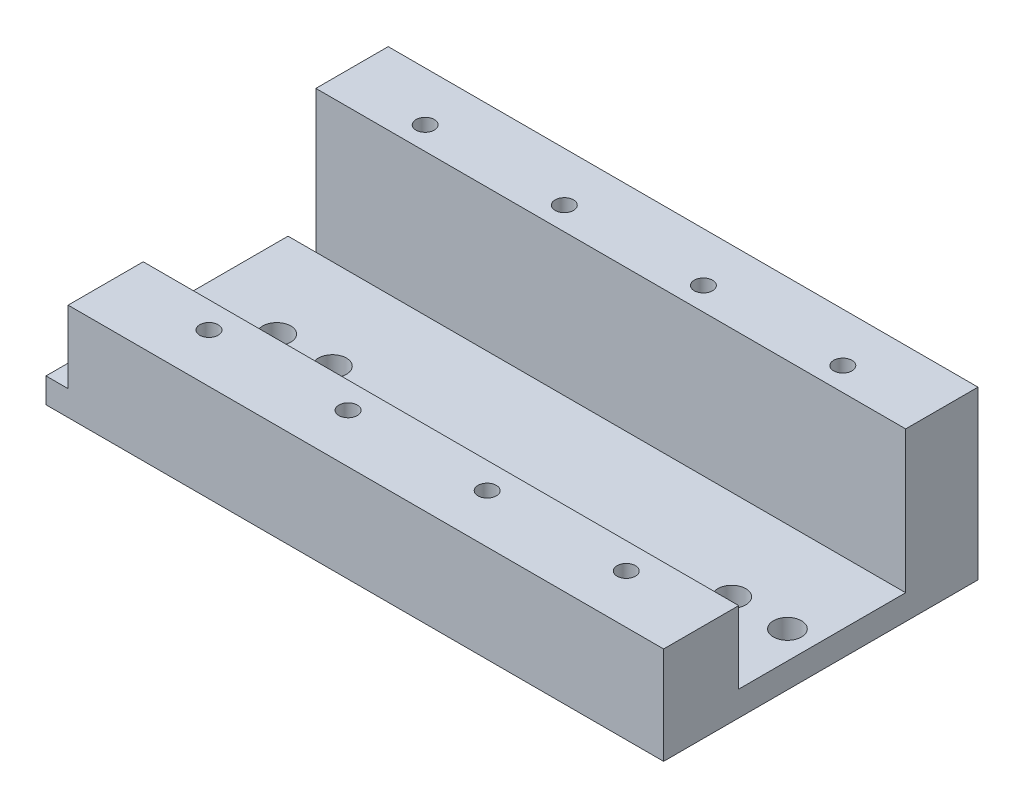
SolidWorks part; units mm, degrees
ref_plane "Front Plane" through (0, 0, 0) normal (0, 0, 1) x (1, 0, 0)
ref_plane "Top Plane" through (0, 0, 0) normal (0, 1, 0) x (1, 0, 0)
ref_plane "Right Plane" through (0, 0, 0) normal (1, 0, 0) x (0, 0, -1)
sketch "Sketch4" plane through (0, 0, 0) normal (0, 0, 1) x (1, 0, 0)
  line L1 (-89.891, -20.3228) -> (16.109, -20.3228)
  line L2 (-89.891, -20.3228) -> (-89.891, -50.3228)
  line L3 (-89.891, -50.3228) -> (16.109, -50.3228)
  line L4 (16.109, -20.3228) -> (16.109, -50.3228)
  dimension "D1" = 30
  dimension "D2" = 106
extrude "Boss-Extrude2" add sketch "Sketch4" against normal blind 13
sketch "Sketch25" plane through (0, 0, 0) normal (0, 0, 1) x (1, 0, 0)
  line L0 (-89.891, -20.3228) -> (-89.891, -50.3228) construction
  line L1 (-89.891, -24.6013) -> (16.109, -24.6013)
  line L2 (-89.891, -24.6013) -> (-89.891, -33.2013)
  line L3 (-89.891, -33.2013) -> (16.109, -33.2013)
  line L4 (16.109, -24.6013) -> (16.109, -33.2013)
  line L5 (16.109, -50.3228) -> (16.109, -20.3228) construction
  dimension "D1" = 8.6
hole_wizard "M4x0.7 Tapped Hole1" positions "3DSketch1" profile "Sketch27" tap size "M4x0.7" standard "ANSI Metric" end condition through all
sketch3d "3DSketch1"
  line L0 (16.109, -20.3228, -13) -> (16.109, -20.3228, 0) construction
  line L2 (16.109, -20.3228, 0) -> (-89.891, -20.3228, 0) construction
  line L3 (-89.891, -20.3228, -13) -> (-89.891, -20.3228, 0) construction
  point P0 (-74.391, -20.3228, -4.15)
  point P2 (-49.391, -20.3228, -4.15)
  point P4 (0.609, -20.3228, -4.2057)
  point P6 (-24.391, -20.3228, -4.15)
  dimension "D1" = 15.5
  dimension "D2" = 25
  dimension "D5" = 4.15
  dimension "D6" = 4.15
  dimension "D7" = 4.15
  dimension "D8" = 25
  dimension "D9" = 25
  dimension "D10" = 15.5001
cosmetic thread "Hole Thread2" parameters "D1"=8, "D2"=4
cosmetic thread "Hole Thread3" parameters "D1"=8, "D2"=4
cosmetic thread "Hole Thread4" parameters "D1"=8, "D2"=4
cosmetic thread "Hole Thread5" parameters "D1"=8, "D2"=4
sketch "Sketch27" plane through (-74.391, -20.3228, -4.15) normal (1, 0, 0) x (0, 0, 1)
  line L0 (0, 0) -> (0, 30)
  line L1 (0, 30) -> (1.65, 30)
  line L2 (1.65, 30) -> (1.65, 0)
  line L5 (1.65, 0) -> (0, 0)
  line L11 (0, -6.35) -> (0, 107.95) construction
  dimension "Thru Tap Drill Dia." = 3.3
  dimension "Thru Tap Drill Depth" = 30
sketch "Sketch28" plane through (0, 0, 0) normal (0, 0, 1) x (1, 0, 0)
  line L0 (-89.891, -20.3228) -> (-89.891, -50.3228) construction
  line L1 (-89.891, -45.8228) -> (16.109, -45.8228)
  line L2 (-89.891, -45.8228) -> (-89.891, -50.3228)
  line L3 (-89.891, -50.3228) -> (16.109, -50.3228)
  line L4 (16.109, -45.8228) -> (16.109, -50.3228)
  dimension "D1" = 4.5
extrude "Boss-Extrude3" add sketch "Sketch28" along normal blind 43.5
sketch "Sketch32" plane through (-89.891, 0, 0) normal (-1, 0, 0) x (0, 0, 1)
  line L1 (0, -45.8228) -> (43.5, -45.8228)
  line L2 (0, -45.8228) -> (0, -50.3228)
  line L3 (0, -50.3228) -> (43.5, -50.3228)
  line L4 (43.5, -45.8228) -> (43.5, -50.3228)
extrude "Boss-Extrude10" add sketch "Sketch32" along normal blind 5
sketch "Sketch33" plane through (-89.891, 0, 0) normal (-1, 0, 0) x (0, 0, 1)
  line L1 (0, -33.2013) -> (-13, -33.2013)
  line L2 (0, -33.2013) -> (0, -50.3228)
  line L3 (0, -50.3228) -> (-13, -50.3228)
  line L4 (-13, -33.2013) -> (-13, -50.3228)
sketch "Sketch35" plane through (-94.891, 0, 0) normal (-1, 0, 0) x (0, 0, 1)
  line L1 (43.5, -45.8228) -> (-13, -45.8228)
  line L2 (43.5, -45.8228) -> (43.5, -50.3228)
  line L3 (43.5, -50.3228) -> (-13, -50.3228)
  line L4 (-13, -45.8228) -> (-13, -50.3228)
hole_wizard "#8 (0.199) Diameter Hole1" positions "3DSketch3" profile "Sketch38" hole size "#8" standard "Progressive" end condition through all
sketch3d "3DSketch3"
  line L0 (16.109, -45.8228, 43.5) -> (-94.891, -45.8228, 43.5) construction
  line L1 (16.109, -45.8228, 43.5) -> (16.109, -45.8228, 0) construction
  point P0 (-80.6691, -45.8228, 16.25)
  point P2 (11.109, -45.8228, 16.25)
  point P4 (1.109, -45.8228, 16.25)
  point P6 (-70.6691, -45.8228, 16.25)
  dimension "D1" = 27.25
  dimension "D2" = 27.25
  dimension "D3" = 27.25
  dimension "D4" = 27.25
  dimension "D5" = 10
  dimension "D6" = 10
  dimension "D7" = 5
sketch "Sketch38" plane through (-80.6691, -45.8228, 16.25) normal (1, 0, 0) x (0, 0, 1)
  line L0 (0, 0) -> (0, 4.5)
  line L1 (0, 4.5) -> (2.5273, 4.5)
  line L2 (2.5273, 4.5) -> (2.5273, 0)
  line L5 (2.5273, 0) -> (0, 0)
  line L11 (0, -6.35) -> (0, 107.95) construction
  dimension "Thru Hole Dia." = 5.0546
  dimension "Thru Hole Depth" = 4.5
sketch "Sketch44" plane through (0, -45.8228, 0) normal (0, 1, 0) x (1, 0, 0)
  line L0 (16.109, -43.5) -> (16.109, 0) construction
  line L1 (-90.9181, -43.5) -> (16.109, -43.5)
  line L2 (-90.9181, -43.5) -> (-90.9181, -30)
  line L3 (-90.9181, -30) -> (16.109, -30)
  line L4 (16.109, -43.5) -> (16.109, -30)
  dimension "D1" = 13.5
extrude "Boss-Extrude17" add sketch "Sketch44" along normal blind 13
hole_wizard "M4x0.7 Tapped Hole2" positions "3DSketch5" profile "Sketch49" tap size "M4x0.7" standard "ANSI Metric"
sketch3d "3DSketch5"
  line L0 (16.109, -32.8228, 43.5) -> (16.109, -32.8228, 30) construction
  line L1 (-90.9181, -32.8228, 43.5) -> (16.109, -32.8228, 43.5) construction
  point P0 (-74.391, -32.8228, 34.71)
  point P2 (-49.391, -32.8228, 34.71)
  point P4 (-24.391, -32.8228, 34.71)
  point P6 (0.609, -32.8228, 34.71)
  dimension "D1" = 15.5
  dimension "D2" = 8.79
  dimension "D3" = 8.79
  dimension "D4" = 25
  dimension "D5" = 8.79
  dimension "D6" = 25
  dimension "D7" = 25
  dimension "D8" = 8.79
cosmetic thread "Hole Thread6" parameters "D1"=8, "D2"=4
cosmetic thread "Hole Thread7" parameters "D1"=8, "D2"=4
cosmetic thread "Hole Thread8" parameters "D1"=8, "D2"=4
cosmetic thread "Hole Thread9" parameters "D1"=8, "D2"=4
sketch "Sketch49" plane through (-74.391, -32.8228, 34.71) normal (1, 0, 0) x (0, 0, 1)
  line L0 (0, 0) -> (0, 18.4904)
  line L1 (0, 18.4904) -> (1.65, 17.499)
  line L2 (1.65, 17.499) -> (1.65, 0)
  line L5 (1.65, 0) -> (0, 0)
  line L10 (0, 18.4904) -> (-1.65, 17.499) construction
  line L11 (0, -6.35) -> (0, 107.95) construction
  dimension "Tap Drill Dia." = 3.3
  dimension "Tap Drill Depth" = 17.499
  dimension "Drill Angle" = 118
